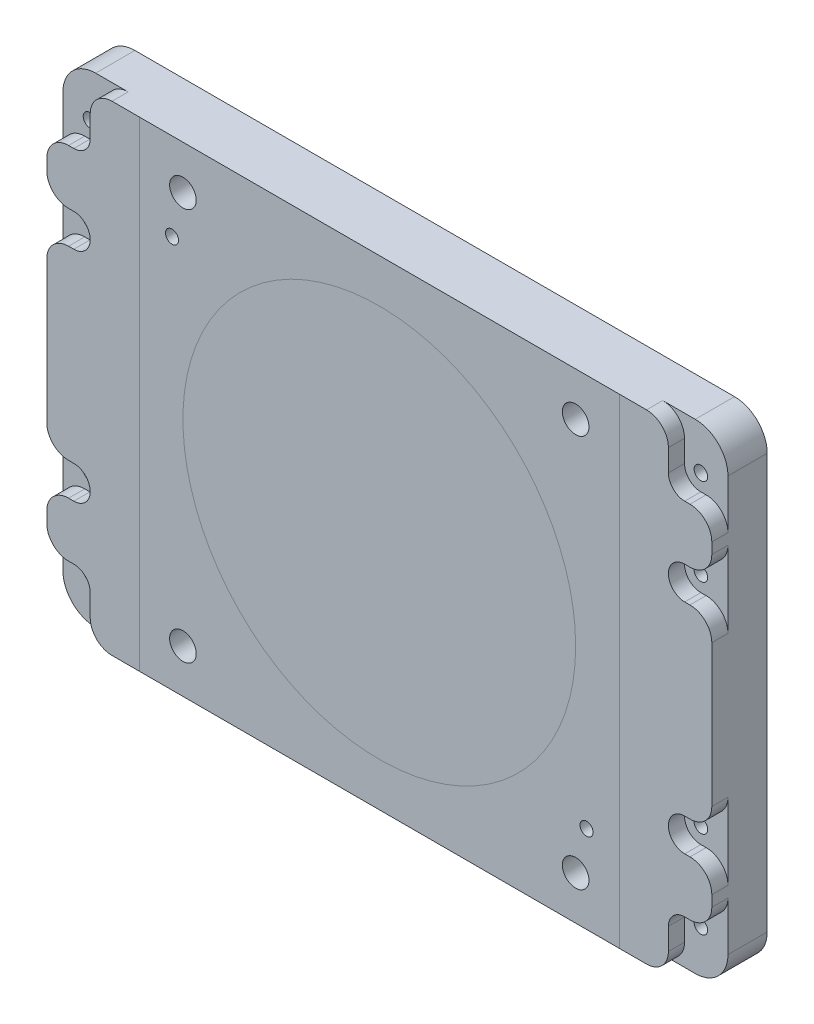
SolidWorks part; units mm, degrees
material "6061 Alloy"
ref_plane "Front Plane" through (0, 0, 0) normal (0, 0, 1) x (1, 0, 0)
ref_plane "Top Plane" through (0, 0, 0) normal (0, 1, 0) x (1, 0, 0)
ref_plane "Right Plane" through (0, 0, 0) normal (1, 0, 0) x (0, 0, -1)
imported_body "Imported3" [suppressed]
imported_body "Imported4" [suppressed]
imported_body "Imported5" [suppressed]
imported_body "Imported6" [suppressed]
ref_plane "Plane2" through (0, 0, 0) normal (0, 0, -1) x (-1, 0, 0)
sketch "Sketch18" plane through (0, 0, 0) normal (0, 0, -1) x (-1, 0, 0)
  line L0 (20, -40) -> (-20, -40)
  line L1 (-50, -10) -> (-50, -5)
  line L2 (-50, -5) -> (-55, 0)
  line L3 (-55, 0) -> (-50, 5)
  line L4 (-50, 5) -> (-50, 100)
  line L5 (-60, 110) -> (-165, 110)
  line L6 (-175, 100) -> (-175, 40)
  line L7 (-165, 30) -> (-155, 30)
  line L8 (-115, -10) -> (-115, -104.2438)
  line L9 (-114.4997, -105.567) -> (-40.5971, -189.3232)
  line L10 (-39.0975, -190) -> (39.0975, -190)
  line L11 (40.5971, -189.3232) -> (114.4997, -105.567)
  line L12 (115, -104.2438) -> (115, -10)
  line L13 (155, 30) -> (165, 30)
  line L14 (175, 40) -> (175, 100)
  line L15 (165, 110) -> (60, 110)
  line L16 (50, 100) -> (50, 5)
  line L17 (50, 5) -> (55, 0)
  line L18 (55, 0) -> (50, -5)
  line L19 (50, -5) -> (50, -10)
  arc A0 (-20, -40) -> (-50, -10) centre (-20, -10) cw
  arc A1 (-50, 100) -> (-60, 110) centre (-60, 100) ccw
  arc A2 (-165, 110) -> (-175, 100) centre (-165, 100) ccw
  arc A3 (-175, 40) -> (-165, 30) centre (-165, 40) ccw
  arc A4 (-155, 30) -> (-115, -10) centre (-155, -10) cw
  arc A5 (-115, -104.2438) -> (-114.4997, -105.567) centre (-113, -104.2438) ccw
  arc A6 (-40.5971, -189.3232) -> (-39.0975, -190) centre (-39.0975, -188) ccw
  arc A7 (39.0975, -190) -> (40.5971, -189.3232) centre (39.0975, -188) ccw
  arc A8 (114.4997, -105.567) -> (115, -104.2438) centre (113, -104.2438) ccw
  arc A9 (115, -10) -> (155, 30) centre (155, -10) cw
  arc A10 (165, 30) -> (175, 40) centre (165, 40) ccw
  arc A11 (175, 100) -> (165, 110) centre (165, 100) ccw
  arc A12 (60, 110) -> (50, 100) centre (60, 100) ccw
  arc A13 (50, -10) -> (20, -40) centre (20, -10) cw
extrude "Boss-Extrude2" add sketch "Sketch18" against normal blind 25.4 separate body
sketch "Sketch19" plane through (0, 0, 0) normal (0, 0, -1) x (-1, 0, 0)
  line L0 (-5, -40) -> (0, -45)
  line L1 (0, -45) -> (5, -40)
  line L2 (5, -40) -> (-5, -40)
extrude "Cut-Extrude2" cut sketch "Sketch19" against normal through all
hole_wizard "Ø5.0 (5) Diameter Hole2" [suppressed] positions "Sketch21" profile "Sketch20" hole size "Ø5.0" standard "ANSI Metric"
sketch "Sketch21" plane through (0, 0, 20) normal (0, 0, 1) x (1, 0, 0)
  point P0 (45, -55)
  point P1 (-45, -55)
  point P2 (-45, -95)
  point P3 (45, -95)
sketch "Sketch20" plane through (45, -55, 20) normal (1, 0, 0) x (0, -1, 0)
  line L0 (0, 0) -> (0, 16.5022)
  line L1 (0, 16.5022) -> (2.5, 15)
  line L2 (2.5, 15) -> (2.5, 0)
  line L5 (2.5, 0) -> (0, 0)
  line L10 (0, 16.5022) -> (-2.5, 15) construction
  line L11 (0, -6.35) -> (0, 107.95) construction
  dimension "Hole Dia." = 5
  dimension "Hole Depth" = 15
  dimension "Drill Angle" = 118
hole_wizard "Ø6.0 (6) Diameter Hole2" [suppressed] positions "Sketch35" profile "Sketch22" hole size "Ø6.0" standard "ANSI Metric"
sketch "Sketch35" plane through (0, 0, 0) normal (0, 0, -1) x (-1, 0, 0)
  point P0 (95, 70)
  point P1 (-95, -70)
  dimension "D1" = 190
  dimension "D2" = 140
sketch "Sketch22" plane through (-95, 70, 0) normal (1, 0, 0) x (0, 1, 0)
  line L0 (0, 0) -> (0, 11.8026)
  line L1 (0, 11.8026) -> (3, 10)
  line L2 (3, 10) -> (3, 0)
  line L5 (3, 0) -> (0, 0)
  line L10 (0, 11.8026) -> (-3, 10) construction
  line L11 (0, -6.35) -> (0, 107.95) construction
  dimension "Hole Dia." = 6
  dimension "Hole Depth" = 10
  dimension "Drill Angle" = 118
hole_wizard "Ø10.2 (10.2) Diameter Hole2" positions "Sketch25" profile "Sketch24" hole size "Ø10.2" standard "ANSI Metric"
sketch "Sketch25" plane through (0, 0, 0) normal (0, 0, -1) x (-1, 0, 0)
  point P0 (-90, -90)
  point P1 (90, -90)
  point P2 (-90, 90)
  point P3 (90, 90)
sketch "Sketch24" plane through (90, -90, 0) normal (1, 0, 0) x (0, 1, 0)
  line L0 (0, 0) -> (0, 25.4)
  line L1 (0, 25.4) -> (6.1, 25.4)
  line L2 (6.1, 25.4) -> (6.1, 0)
  line L5 (6.1, 0) -> (0, 0)
  line L11 (0, -6.35) -> (0, 107.95) construction
  dimension "Thru Hole Dia." = 12.2
  dimension "Thru Hole Depth" = 25.4
hole_wizard "Ø15.0 (15) Diameter Hole2" positions "Sketch27" profile "Sketch26" hole size "Ø15.0" standard "ANSI Metric"
sketch "Sketch27" plane through (0, 0, 0) normal (0, 0, -1) x (-1, 0, 0)
  point P0 (0, -150)
  point P1 (-135, 60)
  point P2 (135, 60)
sketch "Sketch26" plane through (0, -150, 0) normal (1, 0, 0) x (0, 1, 0)
  line L0 (0, 0) -> (0, 25.4)
  line L1 (0, 25.4) -> (7.5, 25.4)
  line L2 (7.5, 25.4) -> (7.5, 0)
  line L5 (7.5, 0) -> (0, 0)
  line L11 (0, -6.35) -> (0, 107.95) construction
  dimension "Thru Hole Dia." = 15
  dimension "Thru Hole Depth" = 25.4
hole_wizard "Ø6.8 (6.8) Diameter Hole2" [suppressed] positions "Sketch29" profile "Sketch28" hole size "Ø6.8" standard "ANSI Metric"
sketch "Sketch29" plane through (0, 0, 0) normal (0, 0, -1) x (-1, 0, 0)
  point P0 (102.5, 22.75)
  point P1 (0, -105)
  point P2 (-102.5, 22.75)
sketch "Sketch28" plane through (-102.5, 22.75, 0) normal (1, 0, 0) x (0, 1, 0)
  line L0 (0, 0) -> (0, 20)
  line L1 (0, 20) -> (3.4, 20)
  line L2 (3.4, 20) -> (3.4, 0)
  line L5 (3.4, 0) -> (0, 0)
  line L11 (0, -6.35) -> (0, 107.95) construction
  dimension "Thru Hole Dia." = 6.8
  dimension "Thru Hole Depth" = 20
hole_wizard "Ø9.0 (9) Diameter Hole2" [suppressed] positions "Sketch31" profile "Sketch30" hole size "Ø9.0" standard "ANSI Metric"
sketch "Sketch31" plane through (0, 0, 0) normal (0, 0, -1) x (-1, 0, 0)
  point P0 (60, -82.5)
  point P1 (-60, -82.5)
  point P2 (120, 95)
  point P3 (-120, 95)
sketch "Sketch30" plane through (-60, -82.5, 0) normal (1, 0, 0) x (0, 1, 0)
  line L0 (0, 0) -> (0, 20)
  line L1 (0, 20) -> (4.5, 20)
  line L2 (4.5, 20) -> (4.5, 0)
  line L5 (4.5, 0) -> (0, 0)
  line L11 (0, -6.35) -> (0, 107.95) construction
  dimension "Thru Hole Dia." = 9
  dimension "Thru Hole Depth" = 20
sketch "Sketch32" plane through (0, 0, 0) normal (0, 0, 1) x (1, 0, 0)
  line L1 (-115, -110) -> (115, -110)
  line L2 (-115, -110) -> (-115, 110)
  line L3 (-115, 110) -> (115, 110)
  line L4 (115, -110) -> (115, 110)
  line L5 (0, 110) -> (0, -110) construction
  line L6 (-115, 0) -> (115, 0) construction
  circle A0 centre (0, 0) radius 300
  point P0 (0, 0)
  dimension "D3" = 600
  dimension "D1" = 230
  dimension "D2" = 220
extrude "Cut-Extrude3" cut sketch "Sketch32" along normal through all contours A0 L4 L1 L2 L3
sketch "Sketch33" plane through (0, 0, 0) normal (0, 0, 1) x (1, 0, 0)
  line L0 (0, -1000) -> (0, 49000) construction
  line L1 (90, 90) -> (140, 90) construction
  line L2 (140, 90) -> (140, -90) construction
  line L3 (140, -90) -> (90, -90) construction
  line L4 (115, 110) -> (137.4, 110)
  line L5 (152.4, 95) -> (152.4, -95)
  line L6 (-137.4, -110) -> (137.4, -110)
  line L8 (-152.4, 95) -> (-152.4, -95)
  line L9 (-115, 110) -> (-137.4, 110)
  line L13 (-60, 110) -> (60, 110)
  line L14 (-115, -100) -> (115, -100)
  line L19 (115, 110) -> (60, 110)
  line L20 (115, -104.2438) -> (115, 110)
  line L21 (110.5882, -110) -> (114.4997, -105.567)
  line L22 (-110.5882, -110) -> (110.5882, -110)
  line L23 (-114.4997, -105.567) -> (-110.5882, -110)
  line L24 (-115, 110) -> (-115, -104.2438)
  line L25 (-60, 110) -> (-115, 110)
  line L26 (-50, 5) -> (-50, 100)
  line L27 (-55, 0) -> (-50, 5)
  line L28 (-50, -5) -> (-55, 0)
  line L29 (-50, -10) -> (-50, -5)
  line L30 (-5, -40) -> (-20, -40)
  line L31 (0, -45) -> (-5, -40)
  line L32 (5, -40) -> (0, -45)
  line L33 (20, -40) -> (5, -40)
  line L34 (50, -5) -> (50, -10)
  line L35 (55, 0) -> (50, -5)
  line L36 (50, 5) -> (55, 0)
  line L37 (50, 100) -> (50, 5)
  line L38 (115, 110) -> (60, 110)
  line L39 (115, -110) -> (115, 110)
  line L43 (-115, 110) -> (-115, -110)
  line L44 (-60, 110) -> (-115, 110)
  line L45 (-50, 5) -> (-50, 100)
  line L46 (-55, 0) -> (-50, 5)
  line L47 (-50, -5) -> (-55, 0)
  line L48 (-50, -10) -> (-50, -5)
  line L49 (-5, -40) -> (-20, -40)
  line L50 (0, -45) -> (-5, -40)
  line L51 (5, -40) -> (0, -45)
  line L52 (20, -40) -> (5, -40)
  line L53 (50, -5) -> (50, -10)
  line L54 (55, 0) -> (50, -5)
  line L55 (50, 5) -> (55, 0)
  line L56 (50, 100) -> (50, 5)
  circle A0 centre (140, 90) radius 3.1
  circle A1 centre (140, -90) radius 3.1
  arc A2 (137.4, 110) -> (152.4, 95) centre (137.4, 95) cw
  arc A3 (152.4, -95) -> (137.4, -110) centre (137.4, -95) cw
  circle A5 centre (-140, -90) radius 3.1
  arc A6 (114.4997, -105.567) -> (115, -104.2438) centre (113, -104.2438) ccw
  arc A7 (-115, -104.2438) -> (-114.4997, -105.567) centre (-113, -104.2438) ccw
  arc A8 (-50, 100) -> (-60, 110) centre (-60, 100) ccw
  arc A9 (-50, -10) -> (-20, -40) centre (-20, -10) ccw
  arc A10 (20, -40) -> (50, -10) centre (20, -10) ccw
  arc A11 (60, 110) -> (50, 100) centre (60, 100) ccw
  arc A14 (-50, 100) -> (-60, 110) centre (-60, 100) ccw
  arc A15 (-50, -10) -> (-20, -40) centre (-20, -10) ccw
  arc A16 (20, -40) -> (50, -10) centre (20, -10) ccw
  arc A17 (60, 110) -> (50, 100) centre (60, 100) ccw
  circle A18 centre (-140, 90) radius 3.1
  arc A19 (-137.4, 110) -> (-152.4, 95) centre (-137.4, 95) ccw
  circle A20 centre (140, 50) radius 3.1
  circle A21 centre (140, -50) radius 3.1
  circle A22 centre (-140, -50) radius 3.1
  circle A23 centre (-140, 50) radius 3.1
  arc A24 (-137.4, -110) -> (-152.4, -95) centre (-137.4, -95) cw
  point P36 (152.4, -110)
  point P66 (-152.4, -110)
  dimension "D3" = 6.2
  dimension "D5" = 15
  dimension "D6" = 110
  dimension "D7" = 40
  dimension "D8" = 40
  dimension "D9" = 15
  dimension "D2" = 140
  dimension "D10" = 10
  dimension "D12" = 304.8
  dimension "D13" = 304.8
  dimension "D1" = 0
extrude "Boss-Extrude3" add sketch "Sketch33" along normal up to surface (25.4 mm away)
sketch "Sketch36" plane through (0, 0, 25.4) normal (0, 0, 1) x (1, 0, 0)
  line L1 (-95, -70) -> (95, -70) construction
  line L2 (-95, -70) -> (-95, 70) construction
  line L3 (-95, 70) -> (95, 70) construction
  line L4 (95, -70) -> (95, 70) construction
  line L5 (0, 70) -> (0, -70) construction
  line L6 (-95, 0) -> (95, 0) construction
  point P0 (0, 0)
  point P5 (-95, 70)
  point P6 (95, -70)
  dimension "D1" = 190
  dimension "D2" = 140
hole_wizard "Ø6.0 (6) Diameter Hole3" positions "Sketch36" profile "Sketch37" hole size "Ø6.0" standard "ANSI Metric"
sketch "Sketch37" plane through (95, -70, 25.4) normal (1, 0, 0) x (0, -1, 0)
  line L0 (0, 0) -> (0, 11.8026)
  line L1 (0, 11.8026) -> (3, 10)
  line L2 (3, 10) -> (3, 0)
  line L5 (3, 0) -> (0, 0)
  line L10 (0, 11.8026) -> (-3, 10) construction
  line L11 (0, -6.35) -> (0, 107.95) construction
  dimension "Hole Dia." = 6
  dimension "Hole Depth" = 10
  dimension "Drill Angle" = 118
sketch "Sketch34" plane through (0, 0, 25.4) normal (0, 0, 1) x (1, 0, 0)
  line L0 (0, -1000) -> (0, 49000) construction
  line L1 (-1000, 0) -> (49000, 0) construction
  line L3 (140, 82.5) -> (152.4, 82.5)
  line L4 (152.4, 95) -> (152.4, -95) construction
  line L5 (152.4, 82.5) -> (152.4, 110)
  line L7 (140, 57.5) -> (152.4, 57.5)
  line L8 (152.4, 57.5) -> (152.4, 42.5)
  line L9 (152.4, 42.5) -> (140, 42.5)
  line L27 (132.5, 90) -> (132.5, 110)
  line L28 (-137.4, 110) -> (137.4, 110) construction
  line L29 (132.5, 110) -> (152.4, 110)
  line L30 (140, -57.5) -> (152.4, -57.5)
  line L31 (152.4, -57.5) -> (152.4, -42.5)
  line L32 (152.4, -42.5) -> (140, -42.5)
  line L33 (132.5, -90) -> (132.5, -110)
  line L34 (132.5, -110) -> (152.4, -110)
  line L35 (152.4, -82.5) -> (152.4, -110)
  line L36 (140, -82.5) -> (152.4, -82.5)
  line L38 (-140, -82.5) -> (-152.4, -82.5)
  line L39 (-152.4, -82.5) -> (-152.4, -110)
  line L40 (-132.5, -110) -> (-152.4, -110)
  line L41 (-132.5, -90) -> (-132.5, -110)
  line L42 (-152.4, -42.5) -> (-140, -42.5)
  line L43 (-152.4, -57.5) -> (-152.4, -42.5)
  line L44 (-140, -57.5) -> (-152.4, -57.5)
  line L45 (-140, 57.5) -> (-152.4, 57.5)
  line L46 (-152.4, 57.5) -> (-152.4, 42.5)
  line L47 (-152.4, 42.5) -> (-140, 42.5)
  line L48 (-132.5, 90) -> (-132.5, 110)
  line L49 (-132.5, 110) -> (-152.4, 110)
  line L50 (-152.4, 82.5) -> (-152.4, 110)
  line L51 (-140, 82.5) -> (-152.4, 82.5)
  arc A0 (132.5, 90) -> (140, 82.5) centre (140, 90) ccw
  arc A1 (140, 57.5) -> (140, 42.5) centre (140, 50) ccw
  arc A8 (140, -57.5) -> (140, -42.5) centre (140, -50) cw
  arc A9 (132.5, -90) -> (140, -82.5) centre (140, -90) cw
  arc A11 (-132.5, -90) -> (-140, -82.5) centre (-140, -90) ccw
  arc A12 (-140, -57.5) -> (-140, -42.5) centre (-140, -50) ccw
  arc A13 (-140, 57.5) -> (-140, 42.5) centre (-140, 50) cw
  arc A14 (-132.5, 90) -> (-140, 82.5) centre (-140, 90) cw
  dimension "D1" = 15
extrude "Cut-Extrude4" cut sketch "Sketch34" against normal offset from surface (7.4 mm away) 18 up to face at (0, 0, 0)
fillet "Fillet1" radius 10 16 edges at (-132.5, 110, 21.7) (-152.4, 82.5, 21.7) (-152.4, 57.5, 21.7) (-152.4, 42.5, 21.7) (-152.4, -42.5, 21.7) (-152.4, -57.5, 21.7) (-152.4, -82.5, 21.7) (-132.5, -110, 21.7) (132.5, 110, 21.7) (152.4, 82.5, 21.7) (152.4, 57.5, 21.7) (152.4, 42.5, 21.7) (152.4, -42.5, 21.7) (152.4, -57.5, 21.7) (152.4, -82.5, 21.7) (132.5, -110, 21.7)
sketch "Sketch38" plane through (0, 0, 25.4) normal (0, 0, 1) x (1, 0, 0)
  line L0 (-122.5, 110) -> (122.5, 110) construction
  line L1 (-110, -110) -> (110, -110)
  line L2 (-110, -110) -> (-110, 110)
  line L3 (-110, 110) -> (110, 110)
  line L4 (110, -110) -> (110, 110)
  line L5 (0, 110) -> (0, -110) construction
  line L6 (-110, 0) -> (110, 0) construction
  circle A0 centre (0, 0) radius 90
  point P0 (0, 0)
  dimension "D2" = 180
  dimension "D1" = 220
split line "Split Line1"
